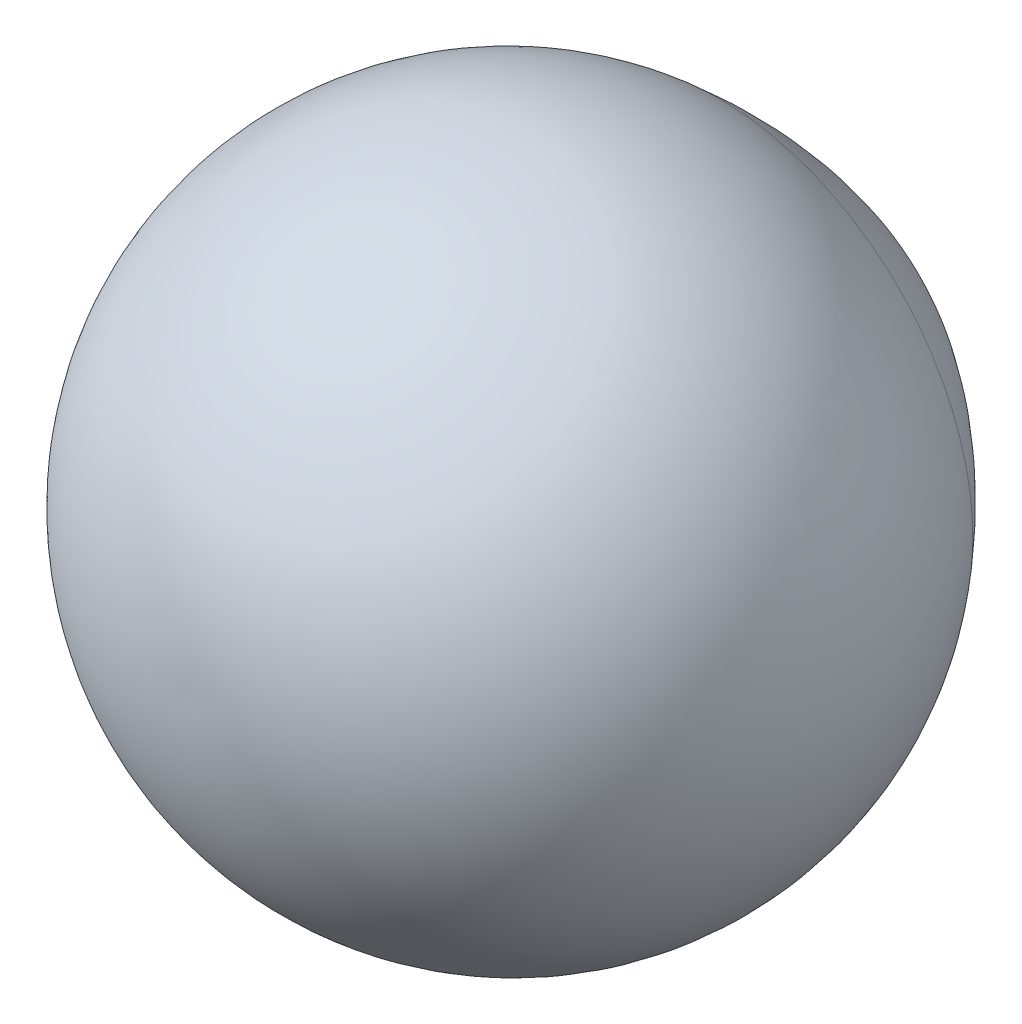
SolidWorks part; units mm, degrees
ref_plane "Front Plane" through (0, 0, 0) normal (0, 0, 1) x (1, 0, 0)
ref_plane "Top Plane" through (0, 0, 0) normal (0, 1, 0) x (1, 0, 0)
ref_plane "Right Plane" through (0, 0, 0) normal (1, 0, 0) x (0, 0, -1)
sketch "Sketch1" plane through (0, 0, 0) normal (0, 0, 1) x (1, 0, 0)
  line L0 (0, 108.4007) -> (0, -55.6652) construction
  line L1 (3.5936, -30.561) -> (3.5936, -37.0369)
  line L2 (3.0116, -38.8627) -> (0, -38.8627)
  line L3 (0, 261.1373) -> (0, -38.8627)
  arc A0 (0, 261.1373) -> (106.0923, 38.5168) centre (3.2307, 126.0869) cw
  arc A1 (106.0923, 38.5168) -> (3.5936, -30.561) centre (-68.7497, 187.3667) cw
  arc A2 (3.7389, -37.7851) -> (3.0116, -38.8627) centre (3.0116, -38.0784) cw
  arc A3 (3.7389, -37.7851) -> (3.5936, -37.0369) centre (5.5936, -37.0369) cw
  dimension "D1" = 2
  dimension "D2" = 300
revolve "Revolve1" add sketch "Sketch1" angle 360 about L0
sketch "Sketch2" plane through (0, 0, 0) normal (0, 0, 1) x (1, 0, 0)
  line L0 (-3.0116, -38.8627) -> (3.0116, -38.8627) construction
  line L1 (0, -362.6278) -> (0, -383.009)
  spline S0 degree 3 poles (0, -38.8627) (16.6042, -67.5249) (-6.6854, -121.99) (2.0201, -207.8959) (-0.4597, -286.7236) (0, -339.6582) (0, -362.6278) knots 0 0 0 0 0.272545 0.511475 0.788633 1 1 1 1
sketch "Sketch4" plane through (0, -38.8627, 0) normal (0, -1, 0) x (1, 0, 0)
  circle A0 centre (0, 0) radius 0.7906
sweep "Sweep1" add profiles "Sketch4" path "Sketch2"
ref_plane "Plane1" through (0, 0, 150) normal (0, 0, 1) x (1, 0, 0)
sketch "Sketch7" plane through (0, 0, 150) normal (0, 0, 1) x (1, 0, 0)
  line L1 (-31.0564, -353.2925) -> (60.8706, -353.2925)
  line L2 (-31.0564, -353.2925) -> (-31.0564, -401.3264)
  line L3 (-31.0564, -401.3264) -> (60.8706, -401.3264)
  line L4 (60.8706, -353.2925) -> (60.8706, -401.3264)
extrude "Cut-Extrude2" cut sketch "Sketch7" against normal through all
sketch "Sketch8" plane through (0, -353.2925, 0) normal (0, -1, 0) x (1, 0, 0)
  circle A0 centre (0, 0) radius 11.3686
extrude "Boss-Extrude1" add sketch "Sketch8" along normal blind 10
scale "Scale1" bodies to scale 108 scale about centroid uniform scaling yes scale factor 3
ref_plane "Plane2" through (0, -863, 0) normal (0, 1, 0) x (1, 0, 0)
sketch "Sketch9" plane through (0, -863, 0) normal (0, 1, 0) x (1, 0, 0)
  line L1 (-72, -50.955) -> (72, -50.955)
  line L2 (-72, -50.955) -> (-72, 50.955)
  line L3 (-72, 50.955) -> (72, 50.955)
  line L4 (72, -50.955) -> (72, 50.955)
  line L5 (-72, -50.955) -> (72, 50.955) construction
  line L6 (-72, 50.955) -> (72, -50.955) construction
  point P0 (0, 0)
sketch "Sketch11" plane through (0, -1307.5012, 0) normal (0, 1, 0) x (1, 0, 0)
  circle A1 centre (-0.0001, 0) radius 34.1057
  circle A2 centre (-0.0001, 0) radius 34.1057
  dimension "D1" = 0
extrude "Cut-Extrude3" cut sketch "Sketch11" along normal up to surface and the other way through all
move or copy body "Body-Move/Copy1" bodies to move or copy 108 copy no rotation origin (0, 85.8461, 0) rotation axis (1, 0, 0) rotation angle 90
